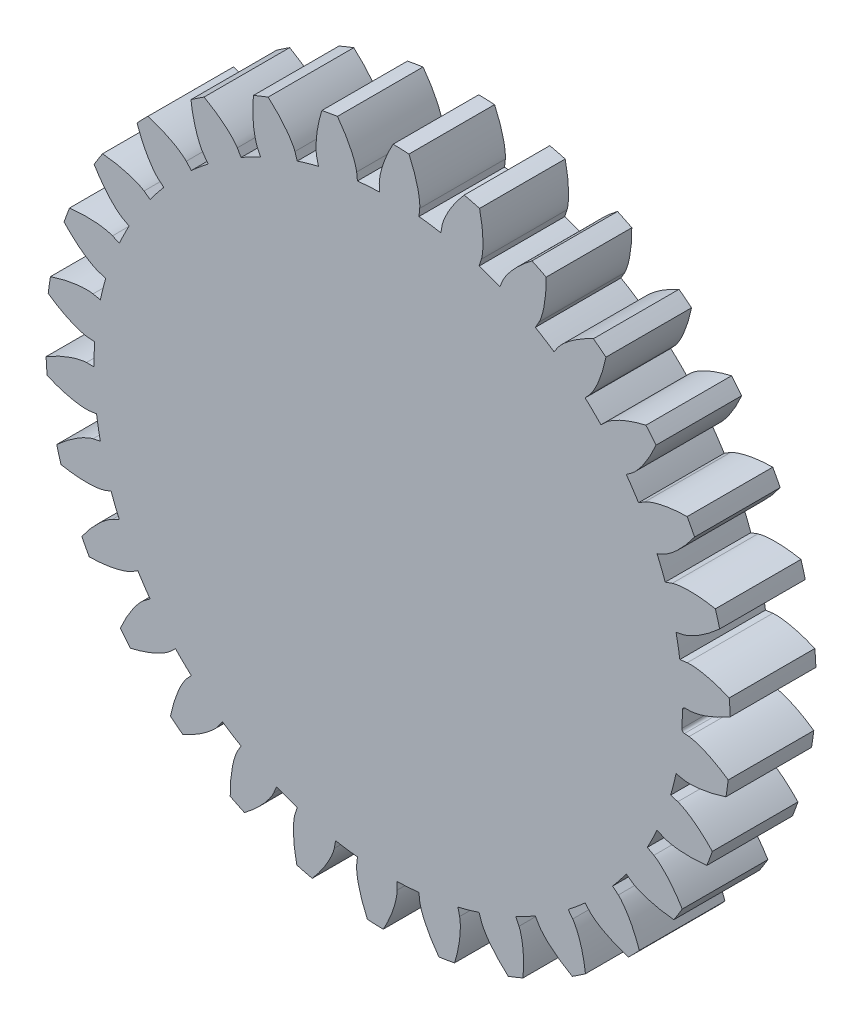
SolidWorks part; units mm, degrees
ref_plane "Front Plane" through (0, 0, 0) normal (0, 0, 1) x (1, 0, 0)
ref_plane "Top Plane" through (0, 0, 0) normal (0, 1, 0) x (1, 0, 0)
ref_plane "Right Plane" through (0, 0, 0) normal (1, 0, 0) x (0, 0, -1)
sketch "Sketch1" plane through (0, 0, 0) normal (0, 0, 1) x (1, 0, 0)
  circle A0 centre (0, 0) radius 101.6
  dimension "D1" = 203.2
extrude "Boss-Extrude1" add sketch "Sketch1" along normal blind 25.4
sketch "Sketch2" plane through (0, 0, 25.4) normal (0, 0, 1) x (1, 0, 0)
  line L0 (87.3125, 0) -> (89.535, 0)
  line L1 (0, 0) -> (101.5285, -3.8116) construction
  line L2 (87.0667, -6.5466) -> (89.2821, -6.7132)
  circle A0 centre (0, 0) radius 95.25 construction
  circle A1 centre (0, 0) radius 89.535 construction
  arc A2 (87.0667, -6.5466) -> (87.3125, 0) centre (0, 0) ccw
  circle A3 centre (0, 0) radius 101.6 construction
  spline S0 degree 4 poles (89.535, 0) (89.6012, 0.0014) (89.7867, 0.0097) (90.1366, 0.0424) (90.7053, 0.12) (91.4255, 0.2544) (92.3495, 0.4685) (93.4276, 0.7723) (94.5995, 1.1599) (96.1733, 1.7583) (97.7153, 2.4386) (99.2246, 3.1882) (100.9536, 4.1375) (102.6461, 5.1509) (104.5743, 6.4228) (106.7109, 7.9853) (108.8118, 9.675) (110.8381, 11.4536) (112.5463, 13.0803) (113.965, 14.521) (115.1166, 15.75) (116.0205, 16.7507) (117.1265, 18.0194) (118.2051, 19.3172) (119.2503, 20.633) (120.4758, 22.249) (121.458, 23.602) (122.3345, 24.8671) (123.0642, 25.9593) (123.6324, 26.8309) (124.0102, 27.4221) (124.6709, 28.4744) (125.1461, 29.2655) (125.6551, 30.1156) (125.8855, 30.5208) (126.0473, 30.7981) knots 0 0 0 0 0 0.005377 0.015084 0.028532 0.04661 0.064855 0.092111 0.119476 0.146842 0.201575 0.228941 0.256307 0.307035 0.361767 0.4165 0.471232 0.525964 0.580697 0.608063 0.635429 0.662795 0.690161 0.744894 0.77226 0.799626 0.854358 0.881725 0.895408 0.909091 0.931818 0.954545 0.977273 1 1 1 1 1 construction
  spline S1 degree 4 poles (89.535, 0) (89.6012, 0.0014) (89.7867, 0.0097) (90.1366, 0.0424) (90.7053, 0.12) (91.4255, 0.2544) (92.3495, 0.4685) (93.4276, 0.7723) (94.5995, 1.1599) (96.1733, 1.7583) (97.7153, 2.4386) (99.2246, 3.1882) (100.9536, 4.1375) (102.6461, 5.1509) (104.5743, 6.4228) (106.7109, 7.9853) (108.8118, 9.675) (110.8381, 11.4536) (112.5463, 13.0803) (113.965, 14.521) (115.1166, 15.75) (116.0205, 16.7507) (117.1265, 18.0194) (118.2051, 19.3172) (119.2503, 20.633) (120.4758, 22.249) (121.458, 23.602) (122.3345, 24.8671) (123.0642, 25.9593) (123.4657, 26.5752) (123.6343, 26.8363) (123.7171, 26.9651) knots 0 0 0 0 0 0.005377 0.015084 0.028532 0.04661 0.064855 0.092111 0.119476 0.146842 0.201575 0.228941 0.256307 0.307035 0.361767 0.4165 0.471232 0.525964 0.580697 0.608063 0.635429 0.662795 0.690161 0.744894 0.77226 0.799626 0.854358 0.881725 0.895408 0.909091 0.909091 0.909091 0.909091 0.909091
  spline S2 degree 4 poles (89.2821, -6.7132) (89.348, -6.7195) (89.5324, -6.7416) (89.8789, -6.8005) (90.4401, -6.9204) (91.1482, -7.1083) (92.0536, -7.391) (93.106, -7.7746) (94.2456, -8.2489) (95.7702, -8.9633) (97.257, -9.7571) (98.7059, -10.6176) (100.359, -11.6936) (101.9709, -12.8308) (103.7986, -14.2435) (105.8122, -15.9616) (107.7808, -17.8038) (109.6683, -19.729) (111.2499, -21.4789) (112.5568, -23.0218) (113.6132, -24.3335) (114.4396, -25.399) (115.4476, -26.7469) (116.426, -28.1218) (117.3699, -29.5122) (118.471, -31.2154) (119.3492, -32.6381) (120.1286, -33.9652) (120.7744, -35.109) (121.2758, -36.0207) (121.6083, -36.6385) (122.1884, -37.7373) (122.603, -38.5618) (123.047, -39.4475) (123.2465, -39.8689) (123.3871, -40.1575) knots 0 0 0 0 0 0.005377 0.015084 0.028532 0.04661 0.064855 0.092111 0.119476 0.146842 0.201575 0.228941 0.256307 0.307035 0.361767 0.4165 0.471232 0.525964 0.580697 0.608063 0.635429 0.662795 0.690161 0.744894 0.77226 0.799626 0.854358 0.881725 0.895408 0.909091 0.931818 0.954545 0.977273 1 1 1 1 1 construction
  spline S3 degree 4 poles (89.2821, -6.7132) (89.348, -6.7195) (89.5324, -6.7416) (89.8789, -6.8005) (90.4401, -6.9204) (91.1482, -7.1083) (92.0536, -7.391) (93.106, -7.7746) (94.2456, -8.2489) (95.7702, -8.9633) (97.257, -9.7571) (98.7059, -10.6176) (100.359, -11.6936) (101.9709, -12.8308) (103.7986, -14.2435) (105.8122, -15.9616) (107.7808, -17.8038) (109.6683, -19.729) (111.2499, -21.4789) (112.5568, -23.0218) (113.6132, -24.3335) (114.4396, -25.399) (115.4476, -26.7469) (116.426, -28.1218) (117.3699, -29.5122) (118.471, -31.2154) (119.3492, -32.6381) (120.1286, -33.9652) (120.7744, -35.109) (121.1287, -35.7532) (121.2773, -36.0262) (121.3502, -36.1609) knots 0 0 0 0 0 0.005377 0.015084 0.028532 0.04661 0.064855 0.092111 0.119476 0.146842 0.201575 0.228941 0.256307 0.307035 0.361767 0.4165 0.471232 0.525964 0.580697 0.608063 0.635429 0.662795 0.690161 0.744894 0.77226 0.799626 0.854358 0.881725 0.895408 0.909091 0.909091 0.909091 0.909091 0.909091
  dimension "D1" = 190.5
  dimension "D2" = 179.07
  dimension "D3" = 174.625
  dimension "D4" = 2.15
  dimension "D5" = 2.15
extrude "Cut-Extrude1" cut sketch "Sketch2" against normal through all and the other way through all
fillet "Fillet1" radius 0.8467 2 edges at (87.3125, 0, 12.7) (87.0667, -6.5466, 12.7)
pattern_circular "CirPattern14" count 30 over 360 about axis through (0, 0, 25.4) along (0, 0, -1) of "Cut-Extrude1"
equation "\"Diametral Pitch,P\" = 4.0"
equation "\"Number of teeth,N\" = 30.0"
equation "\"Pressure angle,phi\" = 20.0deg"
equation "\"Addendum,a\" = 0.25"
equation "\"Dedendum,b\" = 0.3125"
equation "\"Clearance,c\" = 0.0625"
equation "\"Pitch circle diameter,dp\" = 7.5"
equation "\"Base circle diameter,db\" = 7.047694655894313deg"
equation "\"Addendum circle diameter,dca\" = 8.0"
equation "\"Dedendum circle diameter,dcb\" = 6.875"
equation "\"alpha,alpha\" = 0.8539582918412485deg"
equation "\"D1@Sketch1\"=\"Addendum circle diameter,dca\""
equation "\"D1@Sketch2\"=\"Pitch circle diameter,dp\""
equation "\"D2@Sketch2\"=\"Base circle diameter,db\""
equation "\"D3@Sketch2\"=\"Dedendum circle diameter,dcb\""
equation "\"angle btw buttom of teeth and centerline,inv_angle\" = 2.1460417081587515deg"
equation "\"D4@Sketch2\"=\"angle btw buttom of teeth and centerline,inv_angle\""
equation "\"beta,beta\" = 4.292083416317503"
equation "\"D5@Sketch2\"=\"angle btw buttom of teeth and centerline,inv_angle\""
equation "\"D1@CirPattern14\"=\"Number of teeth,N\""
